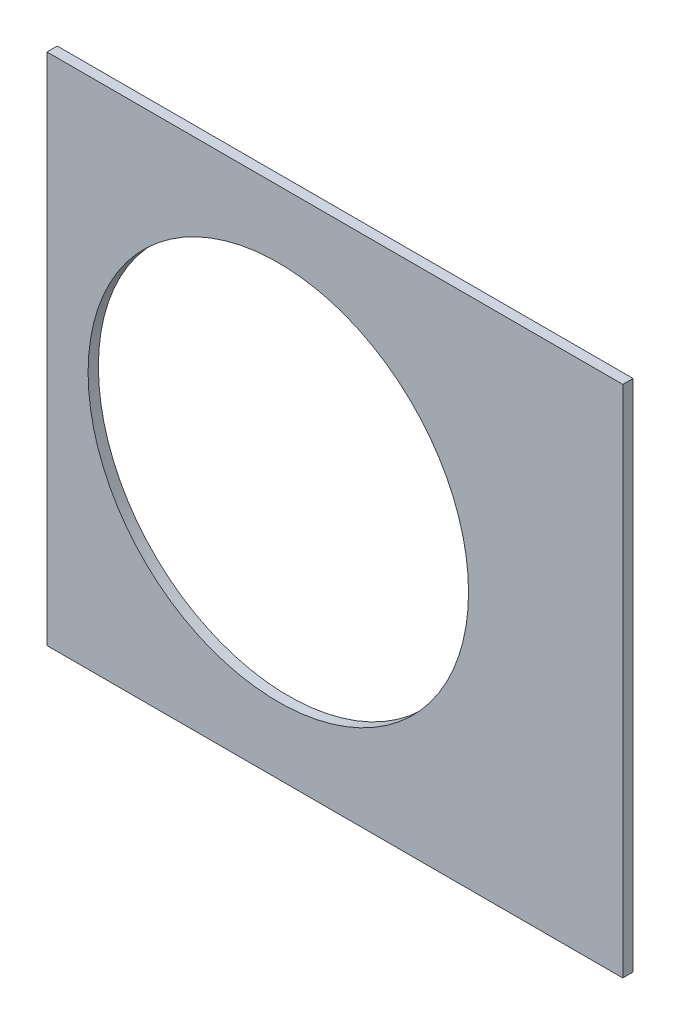
SolidWorks part; units mm, degrees
material "Copper"
ref_plane "Front Plane" through (0, 0, 0) normal (0, 0, 1) x (1, 0, 0)
ref_plane "Top Plane" through (0, 0, 0) normal (0, 1, 0) x (1, 0, 0)
ref_plane "Right Plane" through (0, 0, 0) normal (1, 0, 0) x (0, 0, -1)
sketch "Sketch1" plane through (0, 0, 0) normal (0, 0, 1) x (1, 0, 0)
  line L0 (0, 0) -> (320.3893, 0) construction
  line L1 (0, 0) -> (155.5285, 155.5285) construction
  line L2 (67.2115, 76.1917) -> (8.6967, 17.6769)
  line L3 (8.6967, 17.6769) -> (7.229, 14.1336)
  line L4 (101.4014, -6.35) -> (18.6489, -6.35)
  line L5 (15.1056, -4.8823) -> (18.6489, -6.35)
  line L6 (88.6729, 6.35) -> (27.8605, 6.35)
  line L9 (67.1914, 58.2111) -> (24.1905, 15.2102)
  line L10 (0, 0) -> (40.4486, 97.6516) construction
  line L11 (0, 0) -> (123.4567, -51.1374) construction
  line L18 (8.6967, 17.6769) -> (13.294, 8.6183) construction
  line L19 (18.6489, -6.35) -> (15.4943, 3.3063) construction
  line L20 (27.8605, 6.35) -> (27.7442, 6.7059) construction
  line L21 (24.1905, 15.2102) -> (24.3599, 14.8764) construction
  arc A0 (7.229, 14.1336) -> (15.1056, -4.8823) centre (0, 0) cw
  arc A1 (67.2115, 76.1917) -> (101.4014, -6.35) centre (0, 0) cw
  arc A2 (24.1905, 15.2102) -> (27.8605, 6.35) centre (0, 0) cw
  arc A3 (67.1914, 58.2111) -> (88.6729, 6.35) centre (0, 0) cw
  arc A8 (13.294, 8.6183) -> (15.4943, 3.3063) centre (0, 0) cw construction
  arc A9 (24.3599, 14.8764) -> (27.7442, 6.7059) centre (0, 0) cw construction
  dimension "D1" = 45
  dimension "D3" = 6.35
  dimension "D4" = 15.875
  dimension "D7" = 22.5
  dimension "D8" = 101.6
  dimension "D11" = 12.7
  dimension "D12" = 12.7
  dimension "D2" = 6.35
  dimension "D5" = 67.5
  dimension "D9" = 1.27
  dimension "D10" = 1.27
  dimension "D6" = 12.7
extrude "Boss-Extrude1" add sketch "Sketch1" along normal blind 0.254
sketch "Sketch2" plane through (0, 0, 0.254) normal (0, 0, 1) x (1, 0, 0)
  line L0 (0, 0) -> (101.6, 0) construction
  line L1 (0, 0) -> (71.842, 71.842) construction
  line L3 (0, 0) -> (22.225, 0) construction
  line L4 (0, 0) -> (15.7154, 15.7154) construction
  line L5 (0, 0) -> (95.25, 0) construction
  line L6 (0, 0) -> (92.0044, 24.6525) construction
  arc A0 (101.4014, -6.35) -> (67.2115, 76.1917) centre (0, 0) ccw construction
  circle A1 centre (22.225, 0) radius 4.699
  arc A2 (15.1056, -4.8823) -> (7.229, 14.1336) centre (0, 0) ccw construction
  circle A3 centre (36.195, 0) radius 4.699
  circle A4 centre (61.722, 0) radius 4.699
  circle A5 centre (75.692, 0) radius 4.699
  circle A6 centre (95.25, 0) radius 4.699
  circle A7 centre (15.7154, 15.7154) radius 4.699
  circle A8 centre (25.5937, 25.5937) radius 4.699
  circle A9 centre (43.644, 43.644) radius 4.699
  circle A10 centre (53.5223, 53.5223) radius 4.699
  circle A11 centre (92.0044, 24.6525) radius 4.699
  circle A12 centre (82.4889, 47.625) radius 4.699
  circle A13 centre (67.3519, 67.3519) radius 4.699
  dimension "D3" = 9.398
  dimension "D1" = 45
  dimension "D2" = 6.35
  dimension "D4" = 6.35
  dimension "D5" = 13.97
  dimension "D7" = 13.97
  dimension "D8" = 19.558
  dimension "D9" = 45
  dimension "D10" = 15
  dimension "D11" = 25.527
  dimension "D6" = 2
extrude "Cut-Extrude1" cut sketch "Sketch2" against normal through all
sketch "Sketch3" plane through (0, 0, 0.254) normal (0, 0, 1) x (1, 0, 0)
  line L0 (15.2664, 24.2467) -> (17.0625, 26.0427)
  line L1 (15.2664, 24.2467) -> (15.7154, 23.7977)
  line L2 (17.0625, 26.0427) -> (17.5115, 25.5937)
  line L3 (15.7154, 23.7977) -> (17.5115, 25.5937)
  line L4 (67.2115, 76.1917) -> (8.6967, 17.6769) construction
  line L5 (44.9911, 53.9713) -> (43.195, 52.1753)
  line L6 (44.9911, 53.9713) -> (45.4401, 53.5223)
  line L7 (43.195, 52.1753) -> (43.644, 51.7263)
  line L8 (45.4401, 53.5223) -> (43.644, 51.7263)
  line L9 (27.94, -6.35) -> (30.48, -6.35)
  line L10 (27.94, -6.35) -> (27.94, -5.715)
  line L11 (30.48, -6.35) -> (30.48, -5.715)
  line L12 (27.94, -5.715) -> (30.48, -5.715)
  line L13 (18.6489, -6.35) -> (101.4014, -6.35) construction
  line L14 (67.437, -6.35) -> (69.977, -6.35)
  line L15 (67.437, -6.35) -> (67.437, -5.715)
  line L16 (69.977, -6.35) -> (69.977, -5.715)
  line L17 (67.437, -5.715) -> (69.977, -5.715)
  line L18 (29.2307, 38.211) -> (31.0268, 40.007)
  line L19 (29.2307, 38.211) -> (29.6797, 37.762)
  line L20 (31.0268, 40.007) -> (31.4758, 39.558)
  line L21 (29.6797, 37.762) -> (31.4758, 39.558)
  line L22 (56.845, 65.8253) -> (55.049, 64.0292)
  line L23 (56.845, 65.8253) -> (57.294, 65.3763)
  line L24 (55.049, 64.0292) -> (55.498, 63.5802)
  line L25 (57.294, 65.3763) -> (55.498, 63.5802)
  line L26 (47.6885, -6.35) -> (50.2285, -6.35)
  line L27 (47.6885, -6.35) -> (47.6885, -5.715)
  line L28 (50.2285, -6.35) -> (50.2285, -5.715)
  line L29 (47.6885, -5.715) -> (50.2285, -5.715)
  line L30 (84.201, -6.35) -> (86.741, -6.35)
  line L31 (84.201, -6.35) -> (84.201, -5.715)
  line L32 (86.741, -6.35) -> (86.741, -5.715)
  line L33 (84.201, -5.715) -> (86.741, -5.715)
  line L34 (0, 0) -> (100.7308, 13.2615) construction
  line L35 (0, 0) -> (93.8662, 38.8806) construction
  line L36 (0, 0) -> (80.6047, 61.8502) construction
  line L37 (0, 0) -> (101.6, 0) construction
  line L38 (99.9355, 14.4377) -> (100.267, 11.9194)
  line L39 (99.9355, 14.4377) -> (101.1946, 14.6035)
  line L40 (100.267, 11.9194) -> (101.5261, 12.0852)
  line L41 (101.1946, 14.6035) -> (101.5261, 12.0852)
  line L42 (99.9355, 14.4377) -> (101.5261, 12.0852) construction
  line L43 (100.267, 11.9194) -> (101.1946, 14.6035) construction
  line L44 (93.7655, 37.4643) -> (94.9388, 37.9503)
  line L45 (93.7655, 37.4643) -> (92.7935, 39.811)
  line L46 (94.9388, 37.9503) -> (93.9668, 40.297)
  line L47 (92.7935, 39.811) -> (93.9668, 40.297)
  line L48 (93.7655, 37.4643) -> (93.9668, 40.297) construction
  line L49 (94.9388, 37.9503) -> (92.7935, 39.811) construction
  line L50 (79.3278, 62.4712) -> (80.874, 60.456)
  line L51 (79.3278, 62.4712) -> (80.3354, 63.2443)
  line L52 (80.874, 60.456) -> (81.8816, 61.2292)
  line L53 (80.3354, 63.2443) -> (81.8816, 61.2292)
  line L54 (79.3278, 62.4712) -> (81.8816, 61.2292) construction
  line L55 (80.874, 60.456) -> (80.3354, 63.2443) construction
  line L56 (13.5939, 7.0054) -> (14.5659, 4.6588)
  line L57 (13.5939, 7.0054) -> (14.7672, 7.4914)
  line L58 (14.5659, 4.6588) -> (15.7393, 5.1448)
  line L59 (14.7672, 7.4914) -> (15.7393, 5.1448)
  line L60 (13.5939, 7.0054) -> (15.7393, 5.1448) construction
  line L61 (14.5659, 4.6588) -> (14.7672, 7.4914) construction
  circle A0 centre (15.7154, 15.7154) radius 4.699 construction
  circle A1 centre (43.644, 43.644) radius 4.699 construction
  circle A2 centre (22.225, 0) radius 4.699 construction
  circle A3 centre (61.722, 0) radius 4.699 construction
  arc A4 (101.4014, -6.35) -> (67.2115, 76.1917) centre (0, 0) ccw construction
  arc A9 (15.1056, -4.8823) -> (7.229, 14.1336) centre (0, 0) ccw construction
  circle A10 centre (36.195, 0) radius 4.699 construction
  circle A11 centre (75.692, 0) radius 4.699 construction
  circle A12 centre (25.5937, 25.5937) radius 4.699 construction
  circle A13 centre (53.5223, 53.5223) radius 4.699 construction
  point P75 (14.6666, 6.0751)
  dimension "D2" = 5.715
  dimension "D3" = 2.54
  dimension "D6" = 5.715
  dimension "D8" = 0.635
  dimension "D9" = 5.715
  dimension "D12" = 5.715
  dimension "D4" = 7.5
  dimension "D5" = 22.5
  dimension "D7" = 37.5
  dimension "D10" = 90
  dimension "D11" = 1.27
  dimension "D14" = 0.635
  dimension "D15" = 90
  dimension "D18" = 0.635
  dimension "D19" = 90
  dimension "D22" = 0.635
  dimension "D20" = 1.27
  dimension "D17" = 0.635
  dimension "D13" = 11.4935
  dimension "D16" = 8.509
  dimension "D21" = 11.4935
  dimension "D23" = 8.509
extrude "Cut-Extrude2" cut sketch "Sketch3" against normal through all
sketch "Sketch5" plane through (0, 0, 0.254) normal (0, 0, 1) x (1, 0, 0)
  line L0 (27.8605, 6.35) -> (88.6729, 6.35) construction
  line L1 (69.977, -7.62) -> (84.201, -7.62)
  line L2 (69.977, -7.62) -> (69.977, 7.62)
  line L4 (69.977, 7.62) -> (84.201, 7.62)
  line L5 (84.201, -7.62) -> (84.201, 7.62)
  line L8 (67.437, -5.715) -> (67.437, -6.35) construction
  line L9 (86.741, -6.35) -> (86.741, -5.715) construction
  line L10 (69.977, -6.35) -> (84.201, -6.35) construction
  dimension "D1" = 1.27
  dimension "D2" = 2.54
  dimension "D3" = 2.54
  dimension "D4" = 1.27
extrude "Cut-Extrude5" cut sketch "Sketch5" against normal through all flip side to cut
equation "\"cSep\"= 1.005"
equation "\"D11@Sketch2\"=\"cSep\""
equation "\"cSep2\"= \"D8@Sketch2\""
equation "\"D13@Sketch3\"=\"cSep\"/2-.05"
equation "\"D16@Sketch3\"=\"cSep2\"/2-.05"
equation "\"D21@Sketch3\"=\"cSep\"/2-.05"
equation "\"D23@Sketch3\"=\"cSep2\"/2-.05"
